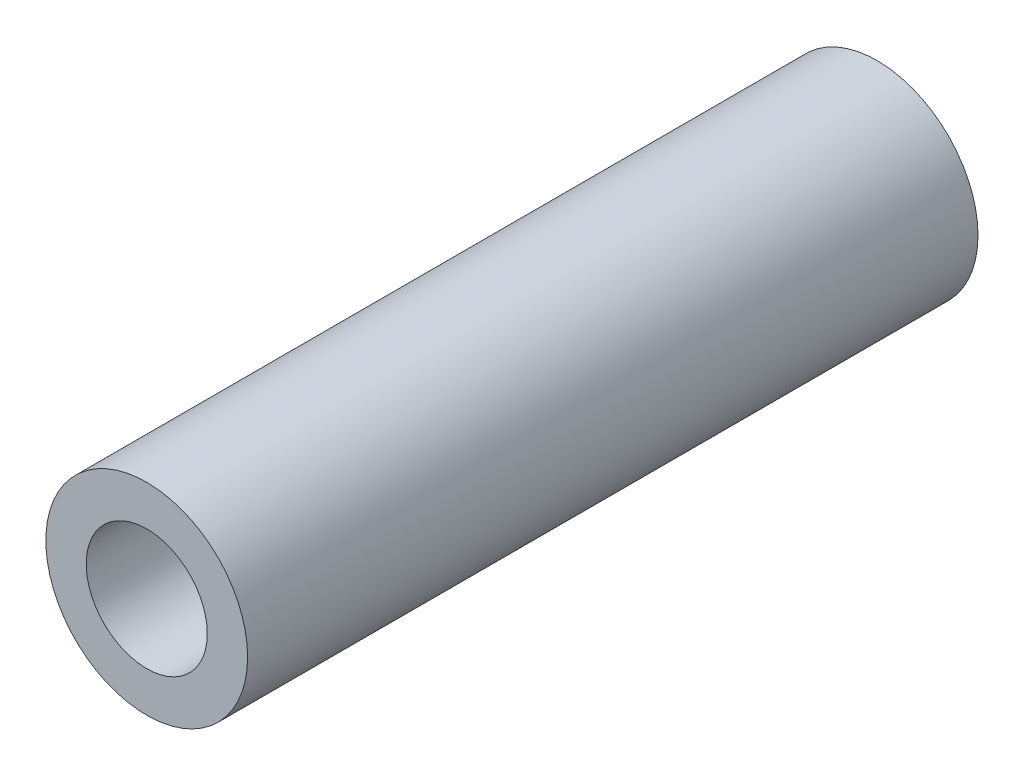
SolidWorks part; units mm, degrees
material "ﾎﾟﾘｵｷｼﾒﾁﾚﾝ(POM)ｱｾﾀｰﾙ共重合体"
ref_plane "Front Plane" through (0, 0, 0) normal (0, 0, 1) x (1, 0, 0)
ref_plane "Top Plane" through (0, 0, 0) normal (0, 1, 0) x (1, 0, 0)
ref_plane "Right Plane" through (0, 0, 0) normal (1, 0, 0) x (0, 0, -1)
sketch "Sketch2" plane through (0, 0, 0) normal (0, 0, 1) x (1, 0, 0)
  circle A0 centre (0, 0) radius 2.5
  circle A1 centre (0, 0) radius 1.5
  dimension "D1" = 3
  dimension "D2" = 5
  dimension "D3" = 5
extrude "Boss-Extrude1" add sketch "Sketch2" along normal blind 18.1
